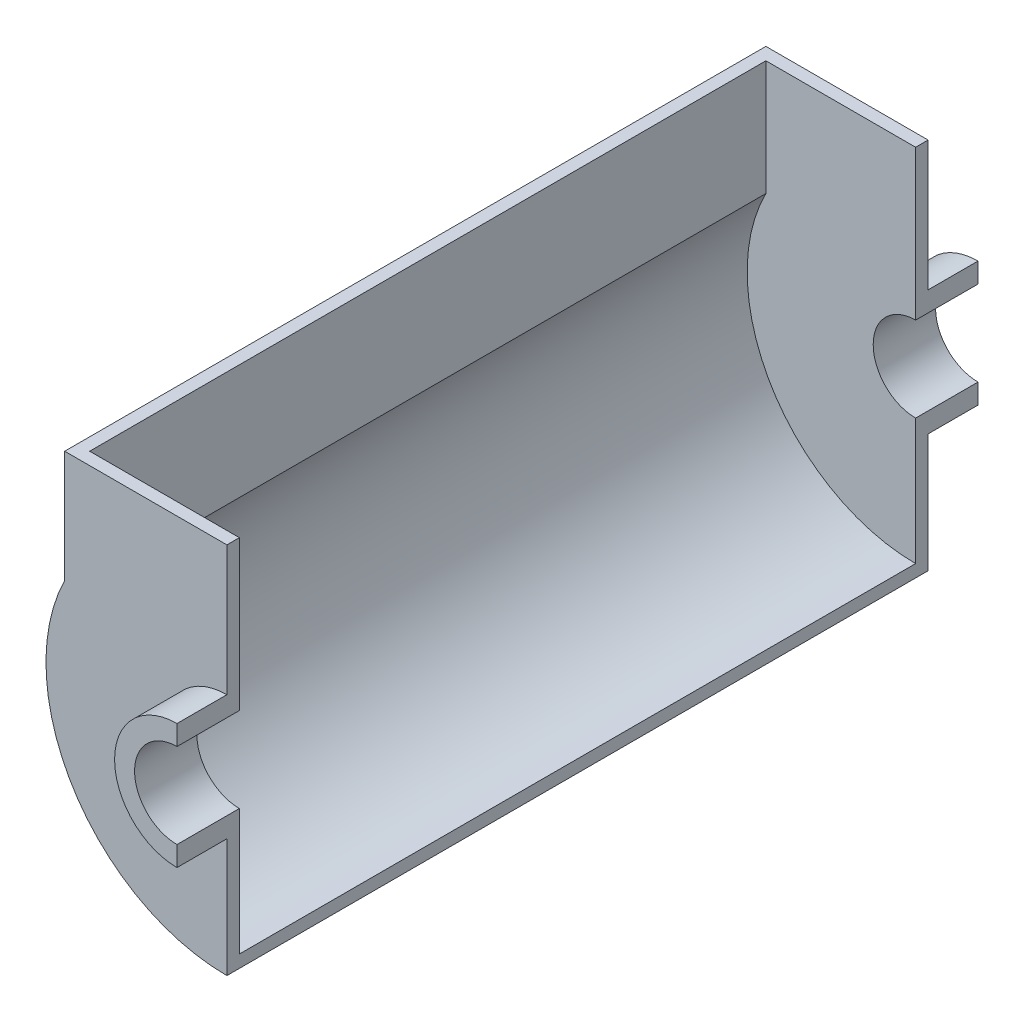
SolidWorks part; units mm, degrees
ref_plane "Front Plane" through (0, 0, 0) normal (0, 0, 1) x (1, 0, 0)
ref_plane "Top Plane" through (0, 0, 0) normal (0, 1, 0) x (1, 0, 0)
ref_plane "Right Plane" through (0, 0, 0) normal (1, 0, 0) x (0, 0, -1)
sketch "Sketch2" plane through (0, 0, 0) normal (0, 0, 1) x (1, 0, 0)
  line L0 (0, 25) -> (0, 17)
  line L1 (0, -17) -> (0, -25)
  arc A0 (0, 25) -> (0, -25) centre (0, 0) ccw
  arc A1 (0, 17) -> (0, -17) centre (0, 0) ccw
  dimension "D1" = 50
  dimension "D2" = 34
extrude "Boss-Extrude1" add sketch "Sketch2" along normal blind 20 and the other way blind 5
sketch "Sketch3" plane through (0, 0, 0) normal (0, 0, 1) x (1, 0, 0)
  line L0 (0, 25) -> (0, 77)
  line L1 (0, 77) -> (-65, 77)
  line L2 (-65, 77) -> (-65, 32.1131)
  line L3 (0, -25) -> (0, -72.5)
  arc A0 (0, 25) -> (0, -25) centre (0, 0) ccw construction
  arc A1 (0, 25) -> (0, -25) centre (0, 0) ccw
  arc A2 (-65, 32.1131) -> (0, -72.5) centre (0, 0) ccw
  point P10 (0, 0)
  dimension "D3" = 72.5
  dimension "D1" = 52
  dimension "D2" = 65
extrude "Boss-Extrude2" add sketch "Sketch3" against normal blind 5
ref_plane "Plane1" through (0, 0, -140.5) normal (0, 0, 1) x (1, 0, 0)
mirror "Mirror3" about plane through (0, 0, -140.5) normal (0, 0, 1) of bodies 102
sketch "Sketch6" plane through (0, 0, -5) normal (0, 0, -1) x (-1, 0, 0)
  line L0 (65, 77) -> (65, 32.1131) construction
  line L1 (65, 77) -> (65, 32.1131)
  line L2 (60, 77) -> (60, 30.9233)
  line L3 (65, 77) -> (60, 77)
  line L4 (0, -72.5) -> (0, -67.5)
  arc A0 (0, -72.5) -> (65, 32.1131) centre (0, 0) ccw construction
  arc A1 (0, -72.5) -> (65, 32.1131) centre (0, 0) ccw
  arc A2 (0, -67.5) -> (60, 30.9233) centre (0, 0) ccw
  dimension "D1" = 5
extrude "Boss-Extrude3" add sketch "Sketch6" along normal up to surface (271 mm away)
